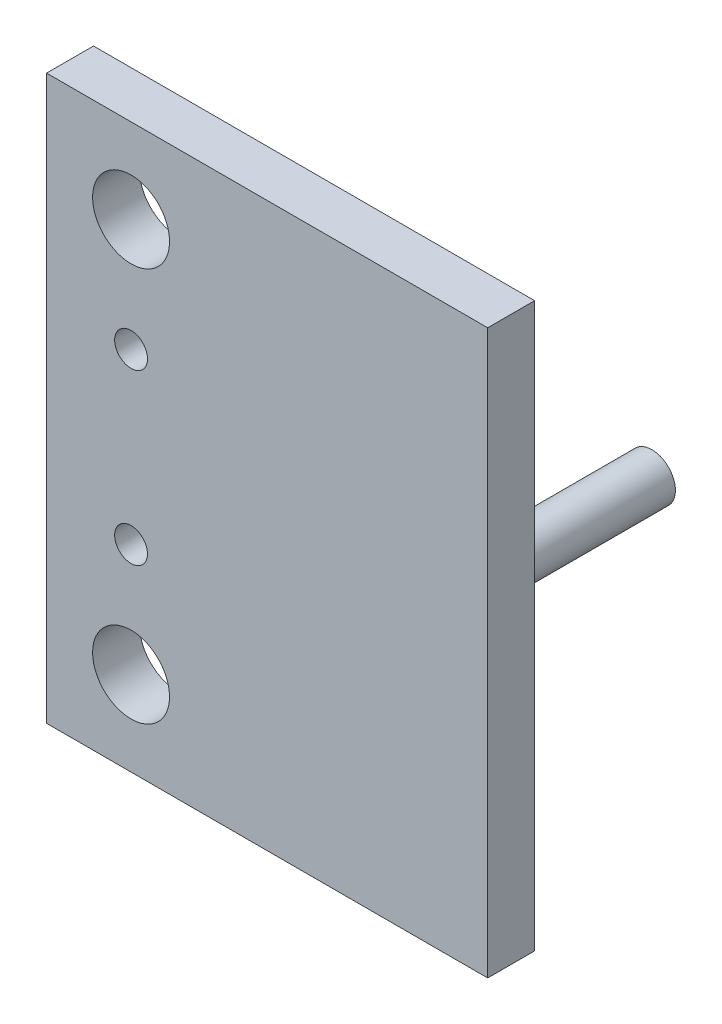
SolidWorks part; units mm, degrees
ref_plane "Front Plane" through (0, 0, 0) normal (0, 0, 1) x (1, 0, 0)
ref_plane "Top Plane" through (0, 0, 0) normal (0, 1, 0) x (1, 0, 0)
ref_plane "Right Plane" through (0, 0, 0) normal (1, 0, 0) x (0, 0, -1)
sketch "Sketch1" plane through (0, 0, 0) normal (1, 0, 0) x (0, 0, -1)
  line L1 (8.0872, -22.3993) -> (13.0872, -22.3993)
  line L2 (8.0872, -22.3993) -> (8.0872, 37.6007)
  line L3 (8.0872, 37.6007) -> (13.0872, 37.6007)
  line L4 (13.0872, -22.3993) -> (13.0872, 37.6007)
  dimension "D1" = 5
  dimension "D2" = 60
extrude "Boss-Extrude1" add sketch "Sketch1" along normal blind 5
sketch "Sketch2" plane through (5, 0, 0) normal (1, 0, 0) x (0, 0, -1)
  line L0 (8.0872, -22.3993) -> (13.0872, -22.3993) construction
  line L1 (8.0872, 37.6007) -> (13.0872, 37.6007)
  line L2 (8.0872, 37.6007) -> (8.0872, -22.3993)
  line L3 (8.0872, -22.3993) -> (13.0872, -22.3993)
  line L4 (13.0872, 37.6007) -> (13.0872, -22.3993)
  dimension "D1" = 5
extrude "Boss-Extrude2" add sketch "Sketch2" along normal blind 20
sketch "Sketch3" plane through (0, 0, -13.0872) normal (0, 0, -1) x (-1, 0, 0)
  line L0 (-25, 37.6007) -> (0, 37.6007) construction
  line L1 (-25, -22.3993) -> (-25, 37.6007) construction
  circle A0 centre (-17.5, 7.6007) radius 2.5
  dimension "D1" = 30
  dimension "D2" = 7.5
extrude "Boss-Extrude3" add sketch "Sketch3" along normal blind 20
sketch "Sketch4" plane through (0, 0, 0) normal (-1, 0, 0) x (0, 0, 1)
  line L1 (-13.0872, 37.6007) -> (-8.0872, 37.6007)
  line L2 (-13.0872, 37.6007) -> (-13.0872, -22.3993)
  line L3 (-13.0872, -22.3993) -> (-8.0872, -22.3993)
  line L4 (-8.0872, 37.6007) -> (-8.0872, -22.3993)
extrude "Boss-Extrude4" add sketch "Sketch4" along normal blind 22
sketch "Sketch5" plane through (0, 0, -13.0872) normal (0, 0, -1) x (-1, 0, 0)
  line L0 (22, 37.6007) -> (22, -22.3993) construction
  line L1 (-25, 37.6007) -> (22, 37.6007) construction
  line L2 (-25, -22.3993) -> (22, -22.3993) construction
  circle A0 centre (13, 28.6007) radius 4.1
  circle A1 centre (13, -13.3993) radius 4.1
  circle A2 centre (13, -1.3993) radius 1.75
  circle A3 centre (13, 16.6007) radius 1.75
  dimension "D1" = 9
  dimension "D2" = 9
  dimension "D3" = 9
  dimension "D4" = 9
  dimension "D5" = 9
  dimension "D6" = 21
  dimension "D7" = 18
extrude "Cut-Extrude1" cut sketch "Sketch5" against normal through all
